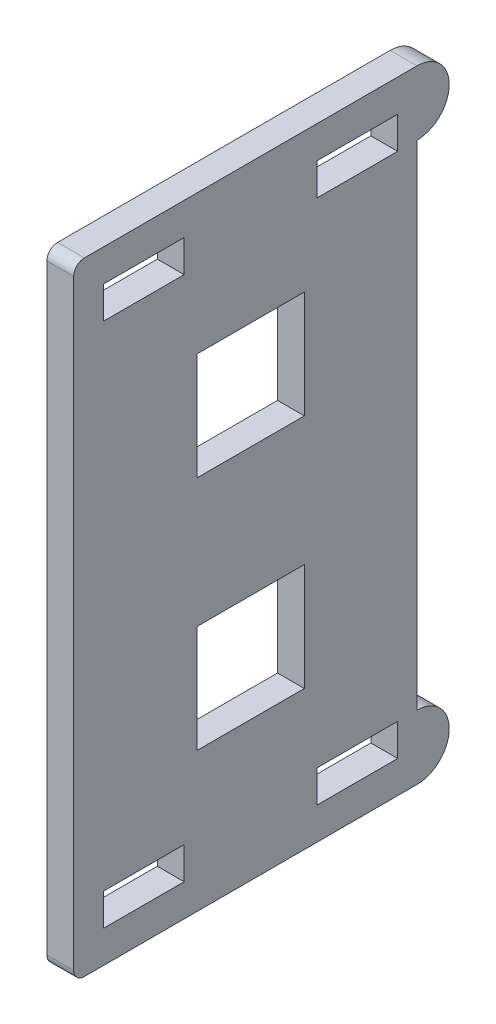
SolidWorks part; units mm, degrees
ref_plane "前视" through (0, 0, 0) normal (0, 0, 1) x (1, 0, 0)
ref_plane "上视" through (0, 0, 0) normal (0, 1, 0) x (1, 0, 0)
ref_plane "右视" through (0, 0, 0) normal (1, 0, 0) x (0, 0, -1)
sketch "草图2" plane through (0, 0, 0) normal (1, 0, 0) x (0, 0, -1)
  line L1 (-17.5, 29) -> (17.5, 29)
  line L2 (-17.5, 29) -> (-17.5, -29)
  line L3 (-17.5, -29) -> (17.5, -29)
  line L4 (17.5, 29) -> (17.5, -29)
  line L5 (-17.5, 29) -> (17.5, -29) construction
  line L6 (-17.5, -29) -> (17.5, 29) construction
  point P0 (0, 0)
  dimension "D1" = 58
  dimension "D2" = 35
extrude "凸台-拉伸1" add sketch "草图2" along normal blind 2.5
sketch "草图4" plane through (0, 0, 0) normal (-1, 0, 0) x (0, 0, 1)
  line L0 (-17.8855, 26) -> (19.6323, 26) construction
  line L1 (-17.5, 29) -> (17.5, 29) construction
  line L2 (-12.7, 26) -> (-5.2, 26)
  line L3 (-5.2, 26) -> (-5.2, 23)
  line L4 (-5.2, 23) -> (-12.7, 23)
  line L5 (-12.7, 23) -> (-12.7, 26)
  line L6 (-17.5, -29) -> (-17.5, 29) construction
  line L7 (7.2, 26) -> (14.7, 26)
  line L8 (14.7, 26) -> (14.7, 23)
  line L9 (14.7, 23) -> (7.2, 23)
  line L10 (7.2, 23) -> (7.2, 26)
  line L11 (17.5, 29) -> (17.5, -29) construction
  line L12 (0, 0) -> (-2.7087, 0) construction
  line L13 (-12.7, -23) -> (-12.7, -26)
  line L14 (7.2, -23) -> (7.2, -26)
  line L15 (-5.2, -26) -> (-5.2, -23)
  line L16 (14.7, -26) -> (14.7, -23)
  line L17 (14.7, -23) -> (7.2, -23)
  line L18 (7.2, -26) -> (14.7, -26)
  line L19 (-12.7, -26) -> (-5.2, -26)
  line L20 (-5.2, -23) -> (-12.7, -23)
  dimension "D1" = 3
  dimension "D2" = 4.8
  dimension "D3" = 3
  dimension "D4" = 7.5
  dimension "D5" = 7.5
  dimension "D6" = 3
  dimension "D7" = 2.8
extrude "切除-拉伸1" cut sketch "草图4" against normal through all
sketch "草图5" plane through (0, 0, 0) normal (-1, 0, 0) x (0, 0, 1)
  line L0 (-13.8103, 26) -> (-12.7631, 26) construction
  line L1 (-17.5, 29) -> (17.5, 29) construction
  line L2 (-14.5, 27.3502) -> (-14.5, 25.8843) construction
  line L3 (-17.5, -29) -> (-17.5, 29) construction
  line L4 (-11.0063, 0) -> (-20.4085, 0) construction
  line L5 (-14.5, 23) -> (-14.5, -23)
  line L6 (-14.5, 0) -> (-17.5, 0)
  line L7 (-17.5, -29) -> (-17.5, 29)
  line L8 (-14.5, 29) -> (-17.5, 29)
  line L9 (0, 0) -> (-4.681, 0) construction
  line L10 (-14.5, -29) -> (-17.5, -29)
  arc A0 (-14.5, 29) -> (-14.5, 23) centre (-14.5, 26) ccw
  arc A1 (-14.5, -29) -> (-14.5, -23) centre (-14.5, -26) cw
  line M9 (-17.5, 29) -> (-17.5, -29)
  line M10 (-17.5, -29) -> (17.5, -29)
  line M12 (17.5, 29) -> (-17.5, 29)
  dimension "D1" = 3
  dimension "D2" = 3
extrude "切除-拉伸2" cut sketch "草图5" against normal through all contours A0 M12 M9 | A0 L7 L6 L5 | A1 L5 L6 M9 | A1 L7 M10
sketch "草图7" plane through (0, 0, 0) normal (-1, 0, 0) x (0, 0, 1)
  line L0 (-12.7, -26) -> (-5.2, -26) construction
  line L1 (-4, -6) -> (6, -6)
  line L2 (-4, -6) -> (-4, -16)
  line L3 (-4, -16) -> (6, -16)
  line L4 (6, -6) -> (6, -16)
  line L5 (-14.5, 23) -> (-14.5, -23) construction
  line L6 (0, 0) -> (-3.3542, 0) construction
  line L7 (-4, 16) -> (6, 16)
  line L8 (6, 6) -> (6, 16)
  line L9 (-4, 6) -> (6, 6)
  line L10 (-4, 6) -> (-4, 16)
  dimension "D1" = 10
  dimension "D2" = 10
  dimension "D3" = 10
  dimension "D4" = 10.5
extrude "切除-拉伸3" cut sketch "草图7" against normal through all
fillet "圆角1" radius 1 2 edges at (1.25, -29, 17.5) (1.25, 29, 17.5)
